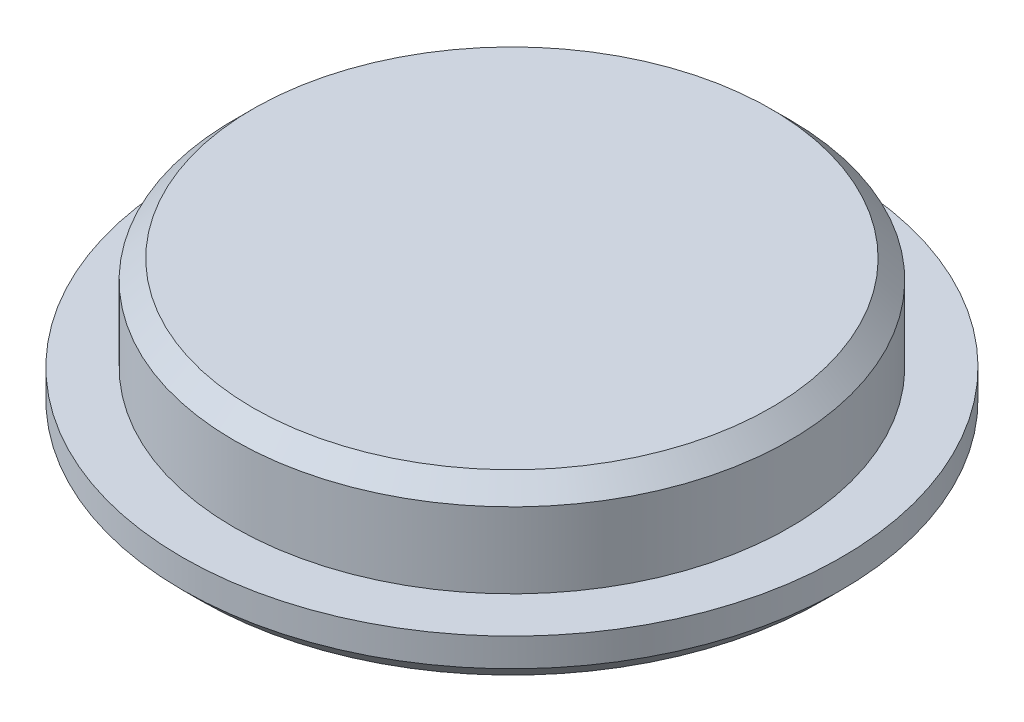
SolidWorks part; units mm, degrees
ref_plane "Front Plane" through (0, 0, 0) normal (0, 0, 1) x (1, 0, 0)
ref_plane "Top Plane" through (0, 0, 0) normal (0, 1, 0) x (1, 0, 0)
ref_plane "Right Plane" through (0, 0, 0) normal (1, 0, 0) x (0, 0, -1)
sketch "Sketch2" plane through (0, 0, 0) normal (0, 0, 1) x (1, 0, 0)
  line L0 (0, 0) -> (33, 0)
  line L1 (0, 0) -> (0, -50000) construction
  line L2 (35, 2) -> (35, 5)
  line L3 (29.5, 5) -> (29.5, 13)
  line L4 (29.5, 5) -> (35, 5)
  line L5 (27.5, 15) -> (0, 15)
  line L6 (0, 15) -> (0, 0)
  line L7 (33, 0) -> (35, 2)
  line L8 (29.5, 13) -> (27.5, 15)
  point P1 (35, 0)
  point P8 (29.5, 15)
revolve "Revolve1" add sketch "Sketch2" angle 360 about L1
